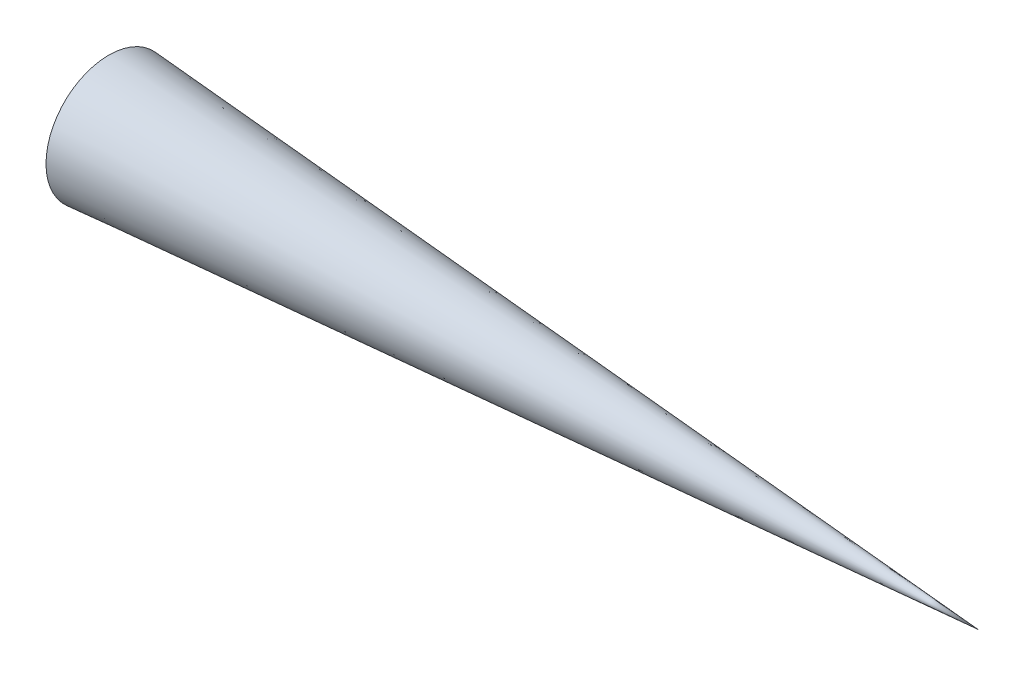
SolidWorks part; units mm, degrees
ref_plane "Front Plane" through (0, 0, 0) normal (0, 0, 1) x (1, 0, 0)
ref_plane "Top Plane" through (0, 0, 0) normal (0, 1, 0) x (1, 0, 0)
ref_plane "Right Plane" through (0, 0, 0) normal (1, 0, 0) x (0, 0, -1)
sketch "Sketch1" plane through (0, 0, 0) normal (0, 0, 1) x (1, 0, 0)
  line L0 (0, 14.505) -> (0, 15.267)
  line L1 (0, 15.267) -> (211.56, 0)
  line L2 (211.56, 0) -> (201.001, 0)
  line L3 (201.001, 0) -> (0, 14.505)
  line L4 (217.7145, 0) -> (-42.8147, 0) construction
  dimension "D1" = 211.56
  dimension "D2" = 0.76
  dimension "D3" = 14.505
revolve "Revolve1" add sketch "Sketch1" angle 360 about L4
